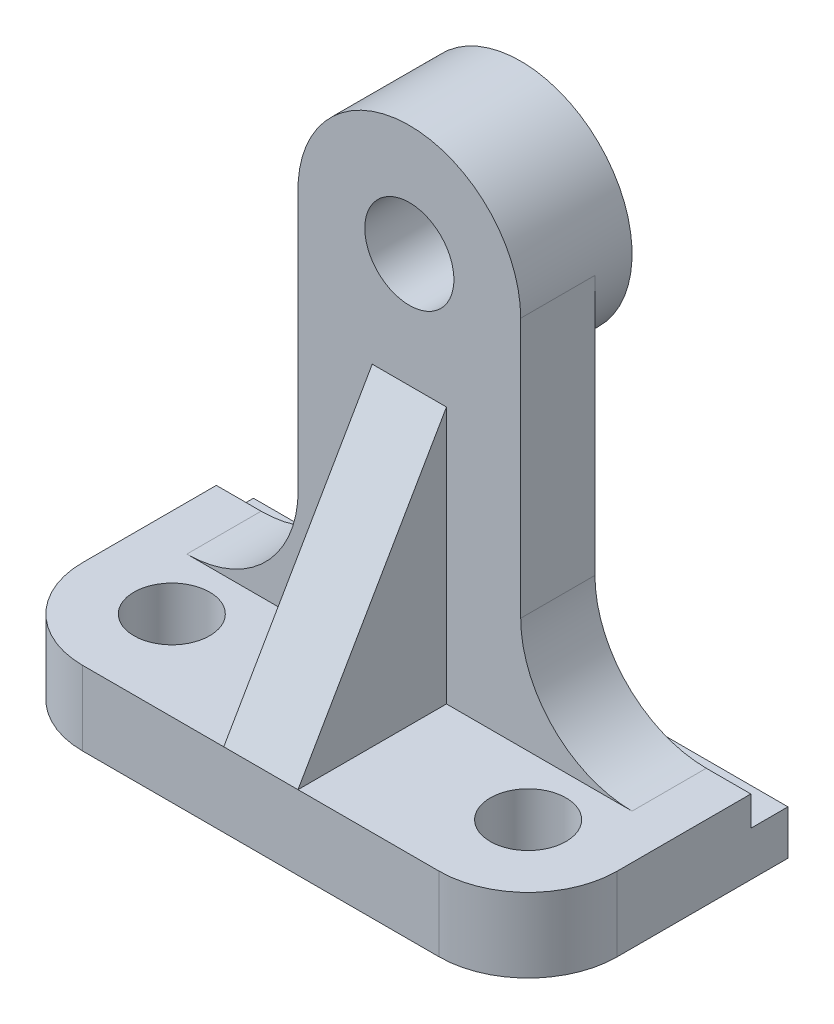
SolidWorks part; units mm, degrees
ref_plane "Front Plane" through (0, 0, 0) normal (0, 0, 1) x (1, 0, 0)
ref_plane "Top Plane" through (0, 0, 0) normal (0, 1, 0) x (1, 0, 0)
ref_plane "Right Plane" through (0, 0, 0) normal (1, 0, 0) x (0, 0, -1)
sketch "Sketch1" plane through (0, 0, 0) normal (0, 1, 0) x (1, 0, 0)
  line L1 (-36, 17.5) -> (36, 17.5)
  line L2 (-36, 17.5) -> (-36, -17.5)
  line L3 (-36, -17.5) -> (36, -17.5)
  line L4 (36, 17.5) -> (36, -17.5)
  line L5 (-36, 17.5) -> (36, -17.5) construction
  line L6 (-36, -17.5) -> (36, 17.5) construction
  point P0 (0, 0)
  dimension "D1" = 72
  dimension "D2" = 35
extrude "Boss-Extrude1" add sketch "Sketch1" along normal blind 10
fillet "Fillet1" radius 12 2 edges at (-36, 5, 17.5) (36, 5, 17.5)
sketch "Sketch3" plane through (36, 0, 0) normal (1, 0, 0) x (0, 0, -1)
  line L1 (17.5, 10) -> (12.5, 10)
  line L2 (17.5, 10) -> (17.5, 6)
  line L3 (17.5, 6) -> (12.5, 6)
  line L4 (12.5, 10) -> (12.5, 6)
  dimension "D1" = 5
  dimension "D2" = 4
extrude "Cut-Extrude1" cut sketch "Sketch3" against normal blind 89
sketch "Sketch6" plane through (0, 0, -12.5) normal (0, 0, -1) x (-1, 0, 0)
  line L0 (14.971, 10) -> (-15, 10)
  line L1 (36, 10) -> (-36, 10) construction
  line L2 (-15, 10) -> (-15, 60)
  line L3 (14.971, 60.9324) -> (14.971, 10)
  arc A0 (-15, 60) -> (14.971, 60.9324) centre (0, 60) cw
  circle A1 centre (0, 60) radius 6
  point P8 (0, 0)
  dimension "D1" = 12
  dimension "D3" = 15
  dimension "D2" = 50
extrude "Boss-Extrude2" add sketch "Sketch6" against normal blind 10
fillet "Fillet2" radius 15 2 edges at (-14.971, 10, -7.5) (15, 10, -7.5)
hole_wizard "M12 Tapped Hole1" positions "Sketch7" profile "Sketch8" tap size "M12" standard "DIN" end condition up to next
sketch "Sketch7" plane through (0, 10, 0) normal (0, 1, 0) x (1, 0, 0)
  point P0 (24, -5.5)
  point P3 (-24, -5.5)
sketch "Sketch8" plane through (24, 10, 5.5) normal (1, 0, 0) x (0, 0, 1)
  line L0 (0, 0) -> (0, 10)
  line L1 (0, 10) -> (5.1, 10)
  line L2 (5.1, 10) -> (5.1, 0)
  line L5 (5.1, 0) -> (0, 0)
  line L11 (0, -6.35) -> (0, 107.95) construction
  dimension "Thru Tap Drill Dia." = 10.2
  dimension "Thru Tap Drill Depth" = 10
cosmetic thread "Hole Thread1" parameters "D2"=12
cosmetic thread "Hole Thread2" parameters "D2"=12
sketch "Sketch11" plane through (0, 0, -12.5) normal (0, 0, -1) x (-1, 0, 0)
  circle A0 centre (0, 60) radius 15
  circle A1 centre (0, 60) radius 6
  dimension "D1" = 30
sketch "Sketch13" plane through (0, 0, -12.5) normal (0, 0, -1) x (-1, 0, 0)
extrude "Boss-Extrude5" add sketch "Sketch11" along normal blind 5 contours A0
sketch "Sketch18" plane through (0, 0, -17.5) normal (0, 0, -1) x (-1, 0, 0)
  circle A0 centre (0, 60) radius 6
extrude "Cut-Extrude2" cut sketch "Sketch18" against normal through all
sketch "Sketch19" plane through (0, 0, 0) normal (1, 0, 0) x (0, 0, -1)
  line L0 (-17.5, 10) -> (2.5, 44.641)
  line L1 (2.5, 60) -> (2.5, 25) construction
  dimension "D1" = 40
rib "Rib1" sketch "Sketch19" sketch "Sketch19" thickness 10 extrusion direction parallel to sketch draft on no parameters "D1"=10
